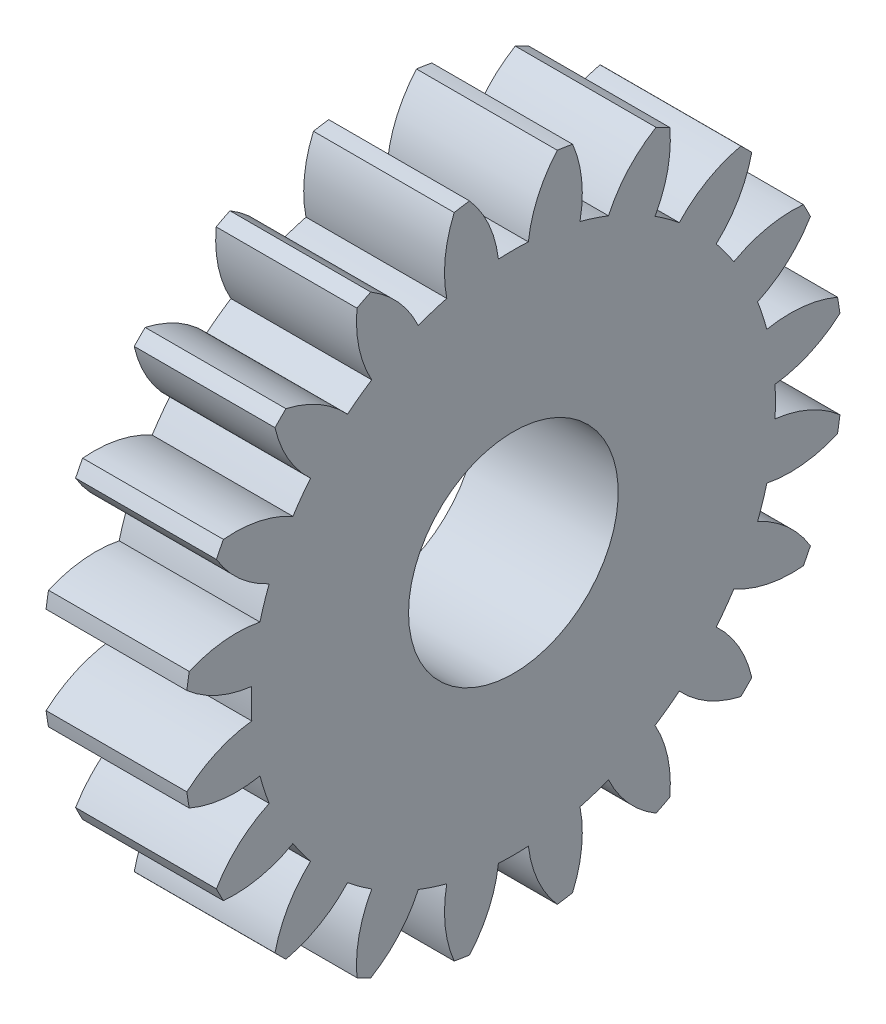
SolidWorks part; units mm, degrees
ref_plane "Plane1" through (0, 0, 0) normal (0, 0, 1) x (1, 0, 0)
ref_plane "Plane2" through (0, 0, 0) normal (0, 1, 0) x (1, 0, 0)
ref_plane "Plane3" through (0, 0, 0) normal (1, 0, 0) x (0, 0, -1)
other "Configuration Table"
sketch "HoldingSke" plane through (0, 0, 0) normal (0, 1, 0) x (1, 0, 0)
  line L0 (0, 0) -> (0.9397, -0.342)
  line L1 (-15, 0) -> (100, 0) construction
  line L2 (0, 0) -> (-2.1039, 2.3779)
  line L3 (0, 0) -> (-11.863, 4.5341)
  line L4 (0, 0) -> (8.1152, 2.9537)
  line L5 (0, 0) -> (-46.8476, -17.4728)
  line L6 (0, 0) -> (-4.1448, -2.7965)
  line L7 (-2.1039, 2.3779) -> (8.6586, 51.2059)
  line L8 (-76.2, 54.61) -> (-74.8, 54.61)
  line L9 (-71.009, 38.7566) -> (-53.1078, 45.2721)
  line L10 (-76.2, 71.12) -> (104.1128, 71.12)
  line L11 (0, 0) -> (-5, 0)
  line L12 (-76.2, 101.6) -> (-76.162, 101.6)
  line L13 (24.9733, 27.94) -> (52.9518, 28.4284)
  line L14 (24.9733, 27.94) -> (24.9743, 27.94)
  line L15 (24.9733, 27.94) -> (100.4006, 29.5858)
  line L16 (-63.627, -1) -> (-12.827, -1)
  circle A0 centre (0, 0) radius 4
  circle A1 centre (0, 0) radius 8.749
  circle A2 centre (0, 0) radius 37.5
  circle A3 centre (0, 0) radius 4
  dimension "MHD" = 17.498
  dimension "Hub_dia" = 75
  dimension "Bore" = 8
  dimension "MBD" = 8
  dimension "Num_teeth" = 20
  dimension "Pitch" = 1
  dimension "Overall_len" = 50
  dimension "Show_teeth" = 20
  dimension "Thickness" = 5
  dimension "OAL" = 50.0001
  dimension "T_dim" = 1.4
  dimension "Ap" = 20
  dimension "H" = 19.05
  dimension "Pitch_radius" = 180.3128
  dimension "Width" = 5
  dimension "Backlash" = 0.038
  dimension "Addendum_fac" = 1
  dimension "Dedendum_fac" = 1.25
  dimension "Clearance_fac" = 0.25
  dimension "Dedendum_add" = 0.001
  dimension "Module" = 1
sketch "BasProSke" plane through (0, 0, 0) normal (0, 1, 0) x (1, 0, 0)
  line L0 (-10, 0) -> (60, 0) construction
  line L1 (0, 0) -> (0, 11)
  line L2 (0, 0) -> (4.7, 0)
  line L3 (4.7, 0) -> (4.7, 11)
  line L4 (4.7, 11) -> (0, 11)
  dimension "Thickness" = 4.7
  dimension "Diameter" = 22
revolve "Base-Revolve" add sketch "BasProSke" angle 360 about L0
sketch "TooCutSke" plane through (0, 0, 0) normal (1, 0, 0) x (0, 0, -1)
  line L1 (0, 0) -> (0, 107) construction
  line L2 (0, 0) -> (-0.8511, 9.9637) construction
  line L3 (0, 0) -> (-3.1206, 19.7028) construction
  line L4 (-0.8511, 9.9637) -> (-1.5603, 9.8514) construction
  arc A0 (0.4999, 8.7347) -> (-0.4999, 8.7347) centre (0, 0) ccw
  arc A1 (1.4852, 10.9249) -> (-1.4852, 10.9249) centre (0, 0) ccw
  circle A2 centre (0, 0) radius 10 construction
  circle A3 centre (0, 0) radius 9.3969 construction
  arc A4 (-0.4999, 8.7347) -> (-1.4852, 10.9249) centre (-4.4722, 8.2645) ccw
  arc A5 (1.4852, 10.9249) -> (0.4999, 8.7347) centre (4.4722, 8.2645) ccw
  dimension "Root_dia" = 17.498
  dimension "Overcut_dia" = 22.0508
  dimension "Pitch_dia" = 20
  dimension "Base_dia" = 18.7939
  dimension "Flank_rad" = 4
  dimension "Half_ang" = 9
  dimension "Half_CT" = 0.7181
extrude "ToothCut" cut sketch "TooCutSke" along normal through all
fillet "Breaks" [suppressed] radius 0.02
fillet "RootFillets" [suppressed] radius 0.251
pattern_circular "TeethCuts" count 20 every 18 about axis through (-10, 0, 0) along (1, 0, 0) of "ToothCut", "RootFillets", "Breaks"
sketch "HubNeaOneSke" plane through (0, 0, 0) normal (-1, 0, 0) x (0, 0, 1)
  circle A0 centre (0, 0) radius 8.749
  dimension "Diameter" = 17.498
extrude "HubNearOne" [suppressed] add sketch "HubNeaOneSke" along normal blind 45.3001
sketch "HubNeaBotSke" plane through (0, 0, 0) normal (-1, 0, 0) x (0, 0, 1)
  circle A0 centre (0, 0) radius 8.749
  dimension "Diameter" = 17.498
extrude "HubNearBoth" [suppressed] add sketch "HubNeaBotSke" along normal blind 22.65
ref_plane "FarPln" through (4.7, 0, 0) normal (1, 0, 0) x (0, 0, -1)
sketch "HubFarSke" plane through (4.7, 0, 0) normal (1, 0, 0) x (0, 0, -1)
  circle A0 centre (0, 0) radius 8.749
  dimension "Diameter" = 17.498
extrude "HubFar" [suppressed] add sketch "HubFarSke" along normal blind 22.65
sketch "BorSke" plane through (0, 0, 0) normal (1, 0, 0) x (0, 0, -1)
  circle A0 centre (0, 0) radius 3.5
  dimension "Diameter" = 7
extrude "Bore" cut sketch "BorSke" along normal mid plane 100.0001
sketch "KeySke" plane through (0, 0, 0) normal (1, 0, 0) x (0, 0, -1)
  line L0 (-1.5, 0) -> (-1.5, 5.4)
  line L1 (-1.5, 5.4) -> (1.5, 5.4)
  line L2 (1.5, 5.4) -> (1.5, 0)
  line L3 (0, 0) -> (0, 34) construction
  line L4 (-1.5, 0) -> (1.5, 0)
  dimension "Offset" = 5.4
  dimension "Width" = 3
extrude "Keyway" [suppressed] cut sketch "KeySke" along normal mid plane 100.0001
pattern_circular "Keyway2" [suppressed] count 2 every 90 about axis through (-10, 0, 0) along (1, 0, 0)
equation "' \"Module@HoldingSke\" = 6.35"
equation "' \"Num_teeth@HoldingSke\" = 12"
equation "' \"Ap@HoldingSke\" =  20"
equation "' \"Ap@HoldingSke\" = 20"
equation "' \"Width@HoldingSke\" = 0.5 * 25.4"
equation "' \"Hub_dia@HoldingSke\"= 1 * 25.4"
equation "' \"Hub_dia@HoldingSke\" = 1 * 25.4"
equation "' \"Overall_len@HoldingSke\" = 1.0 * 25.4"
equation "' \"Bore@HoldingSke\" = 0.75 * 25.4"
equation "' \"T_dim@HoldingSke\" = 0.1 * 25.4"
equation "' \"Width@KeySke\" = 0.25 * 25.4"
equation "' \"Show_teeth@HoldingSke\" = 13"
equation "' \"Backlash@HoldingSke\" = 0.009 * 25.4"
equation "' \"Addendum_fac@HoldingSke\" = 1.0"
equation "' \"Dedendum_fac@HoldingSke\" = 1.25"
equation "' \"Dedendum_add@HoldingSke\" = 0.00005 * 25.4"
equation "' \"Clearance_fac@HoldingSke\" = 0.25"
equation "\"Pitch@HoldingSke\" = 1 / \"Module@HoldingSke\""
equation "\"Overcut_dia@TooCutSke\" = (\"Num_teeth@HoldingSke\" + 2 * \"Addendum_fac@HoldingSke\") / \"Pitch@HoldingSke\" + 0.002 * 25.4"
equation "\"Pitch_dia@TooCutSke\" = \"Num_teeth@HoldingSke\" / \"Pitch@HoldingSke\""
equation "\"Base_dia@TooCutSke\" = \"Num_teeth@HoldingSke\" / \"Pitch@HoldingSke\" * cos((\"Ap@HoldingSke\"  * 3.14159265 / 180))"
equation "\"Root_dia@TooCutSke\" = (\"Num_teeth@HoldingSke\" + 2) / \"Pitch@HoldingSke\" - 2 * (\"Addendum_fac@HoldingSke\" + \"Dedendum_fac@HoldingSke\") / \"Pitch@HoldingSke\" - \"Dedendum_add@HoldingSke\" * 2"
equation "\"Half_ang@TooCutSke\" = 180 / \"Num_teeth@HoldingSke\""
equation "\"Half_CT@TooCutSke\" = \"Num_teeth@HoldingSke\" / \"Pitch@HoldingSke\" * sin((3.14159265 / 2 / \"Num_teeth@HoldingSke\")) / 2 - 7 * \"Backlash@HoldingSke\" / 4"
equation "\"Flank_rad@TooCutSke\" = \"Num_teeth@HoldingSke\" / \"Pitch@HoldingSke\" / 5"
equation "\"Radius@RootFillets\" = \"Clearance_fac@HoldingSke\" / \"Pitch@HoldingSke\" + \"Dedendum_add@HoldingSke\""
equation "\"Break_rad@Breaks\" = 0.02 / \"Pitch@HoldingSke\""
equation "\"Thickness@HoldingSke\" = \"Width@HoldingSke\""
equation "\"OAL@HoldingSke\" = \"Thickness@HoldingSke\""
equation "\"MHD@HoldingSke\" = (\"Num_teeth@HoldingSke\" + 2) / \"Pitch@HoldingSke\" - 2 * (\"Addendum_fac@HoldingSke\" + \"Dedendum_fac@HoldingSke\")  / \"Pitch@HoldingSke\" - \"Dedendum_add@HoldingSke\" * 2"
equation "\"MBD@HoldingSke\" = (\"Num_teeth@HoldingSke\" + 2) / \"Pitch@HoldingSke\" - 2 * (\"Addendum_fac@HoldingSke\" + \"Dedendum_fac@HoldingSke\")  / \"Pitch@HoldingSke\" - \"Dedendum_add@HoldingSke\" * 2 - 0.002 * 25.4"
equation "\"MHD@HoldingSke\" = ((sgn( \"MHD@HoldingSke\" - \"Hub_dia@HoldingSke\" )-1)*( \"MHD@HoldingSke\" - \"Hub_dia@HoldingSke\" ))/-2+ \"Hub_dia@HoldingSke\""
equation "\"MBD@HoldingSke\" = ((sgn( \"MBD@HoldingSke\" - \"Bore@HoldingSke\" )-1)*( \"MBD@HoldingSke\" - \"Bore@HoldingSke\" ))/-2+ \"Bore@HoldingSke\""
equation "\"OAL@HoldingSke\" = ((sgn( \"OAL@HoldingSke\" - \"Overall_len@HoldingSke\" )+1)*( \"OAL@HoldingSke\" - \"Overall_len@HoldingSke\" ))/2 + \"Overall_len@HoldingSke\" + 0.000002 * 25.4"
equation "\"Num_teeth@TeethCuts\" = int( \"Show_teeth@HoldingSke\" ) + 1"
equation "\"Num_teeth@TeethCuts\" = ((sgn( \"Num_teeth@TeethCuts\" - \"Num_teeth@HoldingSke\" )-1)*( \"Num_teeth@TeethCuts\" - \"Num_teeth@HoldingSke\" ))/-2+ \"Num_teeth@HoldingSke\""
equation "\"Num_teeth@TeethCuts\" = ((sgn( \"Num_teeth@TeethCuts\" - 2.0)+1)*( \"Num_teeth@TeethCuts\" - 2.0))/2 +2.0"
equation "\"Angle@TeethCuts\" = 360.0 / \"Num_teeth@HoldingSke\""
equation "\"Diameter@BasProSke\" = (\"Num_teeth@HoldingSke\" + 2 * \"Addendum_fac@HoldingSke\") / \"Pitch@HoldingSke\""
equation "' \"Fillet_rad@BasProSke\" =  \"Thickness@HoldingSke\" * 0.05"
equation "' \"Fillet_rad@BasProSke\" = \"Thickness@HoldingSke\" * 0.05"
equation "\"MHD@HoldingSke\" = ((sgn( \"MHD@HoldingSke\" - \"Root_dia@TooCutSke\" )-1)*( \"MHD@HoldingSke\" - \"Root_dia@TooCutSke\" ))/-2+ \"Root_dia@TooCutSke\""
equation "\"Diameter@HubNeaOneSke\" = \"MHD@HoldingSke\""
equation "\"Length@HubNearOne\" = \"OAL@HoldingSke\" - \"Thickness@BasProSke\""
equation "\"Diameter@HubNeaBotSke\" = \"MHD@HoldingSke\""
equation "\"Length@HubNearBoth\" = ( \"OAL@HoldingSke\" - \"Thickness@BasProSke\" ) / 2.0"
equation "\"Thickness@FarPln\" = \"Thickness@BasProSke\""
equation "\"Diameter@HubFarSke\" = \"MHD@HoldingSke\""
equation "\"Length@HubFar\" = ( \"OAL@HoldingSke\" - \"Thickness@BasProSke\" ) / 2.0"
equation "\"D1@Bore\" = \"OAL@HoldingSke\" * 2.0"
equation "\"D1@Keyway\" = \"OAL@HoldingSke\" * 2.0"
equation "\"Offset@KeySke\" = \"T_dim@HoldingSke\" + \"MBD@HoldingSke\" / 2.0"
